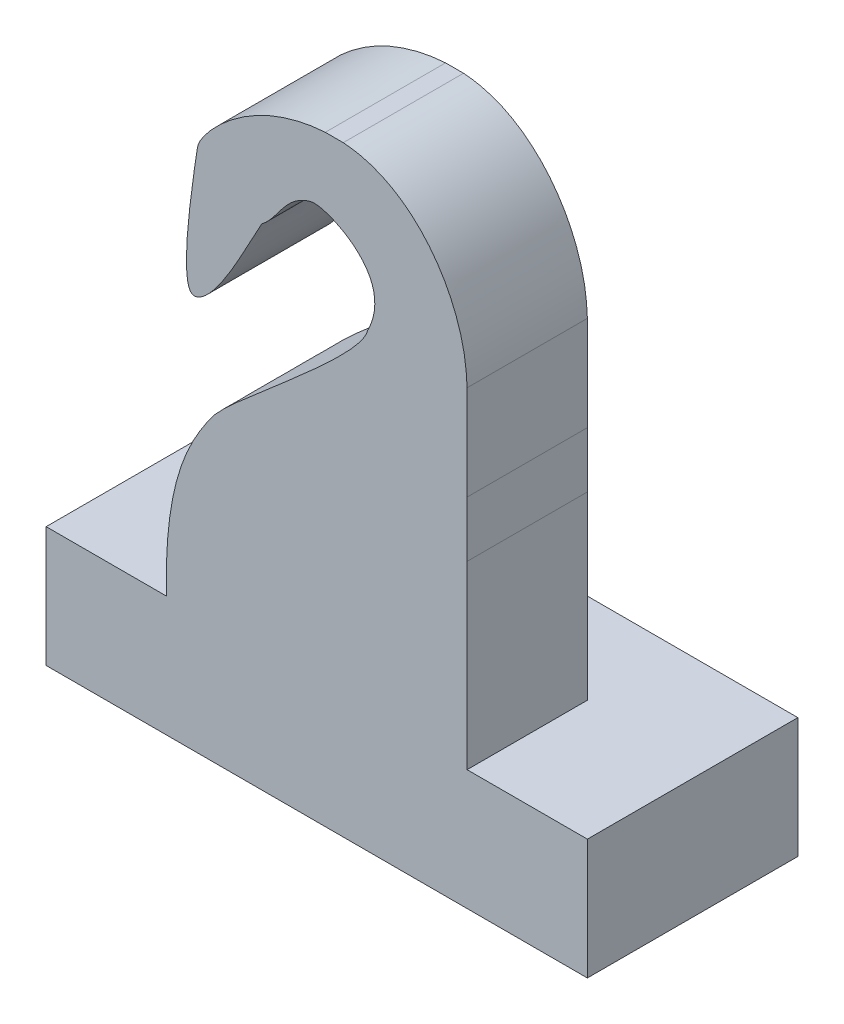
SolidWorks part; units mm, degrees
ref_plane "Front Plane" through (0, 0, 0) normal (0, 0, 1) x (1, 0, 0)
ref_plane "Top Plane" through (0, 0, 0) normal (0, 1, 0) x (1, 0, 0)
ref_plane "Right Plane" through (0, 0, 0) normal (1, 0, 0) x (0, 0, -1)
sketch "Sketch1" plane through (0, 0, 0) normal (0, 1, 0) x (1, 0, 0)
  line L1 (-2.5, -2.5) -> (2.5, -2.5)
  line L2 (-2.5, -2.5) -> (-2.5, 2.5)
  line L3 (-2.5, 2.5) -> (2.5, 2.5)
  line L4 (2.5, -2.5) -> (2.5, 2.5)
  line L5 (-2.5, -2.5) -> (2.5, 2.5) construction
  line L6 (-2.5, 2.5) -> (2.5, -2.5) construction
  point P0 (0, 0)
  dimension "D1" = 5
  dimension "D2" = 5
extrude "Boss-Extrude1" add sketch "Sketch1" along normal blind 2
sketch "Sketch2" plane through (0, 2, 0) normal (0, 1, 0) x (1, 0, 0)
  line L0 (2.5, -2.5) -> (2.5, 2.5) construction
  line L1 (-2.5, -1) -> (2.5, -1)
  line L2 (-2.5, -1) -> (-2.5, 1)
  line L3 (-2.5, 1) -> (2.5, 1)
  line L4 (2.5, -1) -> (2.5, 1)
  line L5 (-2.5, -1) -> (2.5, 1) construction
  line L6 (-2.5, 1) -> (2.5, -1) construction
  point P0 (0, 0)
  dimension "D1" = 2
extrude "Boss-Extrude2" add sketch "Sketch2" along normal blind 8
sketch "Sketch3" plane through (0, 0, 1) normal (0, 0, 1) x (1, 0, 0)
  line L0 (2.5, 10) -> (2.5, 5) construction
  line L1 (2.5, 10) -> (2.5, 2) construction
  line L2 (2.5, 5) -> (-2.5, 5) construction
  line L3 (-2.5, 10) -> (-2.5, 2) construction
  line L4 (-2.5, 10) -> (2.5, 10) construction
  line L5 (-2.5, 2) -> (-2.5, 0)
  line L6 (-2.5, 0) -> (2.5, 0)
  line L7 (2.5, 0) -> (2.5, 5)
  line L8 (-0.9138, 8.1544) -> (0.8464, 7.5) construction
  spline S0 degree 3 poles (-2.5, 2) (-2.5398, 3.6369) (-2.0782, 4.4896) (-1.4649, 5.3539) (0.7334, 7.0438) (0.8464, 7.5) knots 0 0 0 0 0.510186 0.610186 1 1 1 1
  spline S1 degree 3 poles (-0.9138, 8.1544) (-1.1403, 7.764) (-1.6553, 6.6507) (-2.325, 6.4553) (-2.0052, 8.5879) (-1.9506, 8.9369) (-1.0497, 9.9229) (1.4313, 10.1047) (2.4822, 8.629) (2.5186, 6.6088) (2.4901, 5.7819) (2.5, 5) knots 0 0 0 0 0.166355 0.201542 0.335163 0.374434 0.554979 0.601657 0.79454 0.836785 1 1 1 1
  spline S2 degree 3 poles (0.8464, 7.5) (1.2695, 8.3321) (0.1464, 8.9434) (-0.5315, 8.785) (-0.6488, 8.3471) (-0.9138, 8.1544) knots 0 0 0 0 0.263207 0.363207 1 1 1 1
extrude "Cut-Extrude2" cut sketch "Sketch3" against normal through all and the other way through all flip side to cut
sketch "Sketch4" plane through (2.5, 0, 0) normal (1, 0, 0) x (0, 0, -1)
  line L1 (-1, 2) -> (2.5, 2)
  line L2 (-1, 2) -> (-1, 0)
  line L3 (-1, 0) -> (2.5, 0)
  line L4 (2.5, 2) -> (2.5, 0)
extrude "Boss-Extrude3" add sketch "Sketch4" along normal blind 2 and the other way blind 7
sketch "Sketch5" plane through (2.5, 0, 0) normal (1, 0, 0) x (0, 0, -1)
  line L1 (-2.5, 0) -> (-1, 0)
  line L2 (-2.5, 0) -> (-2.5, 2)
  line L3 (-2.5, 2) -> (-1, 2)
  line L4 (-1, 0) -> (-1, 2)
extrude "Cut-Extrude3" cut sketch "Sketch5" against normal through all
